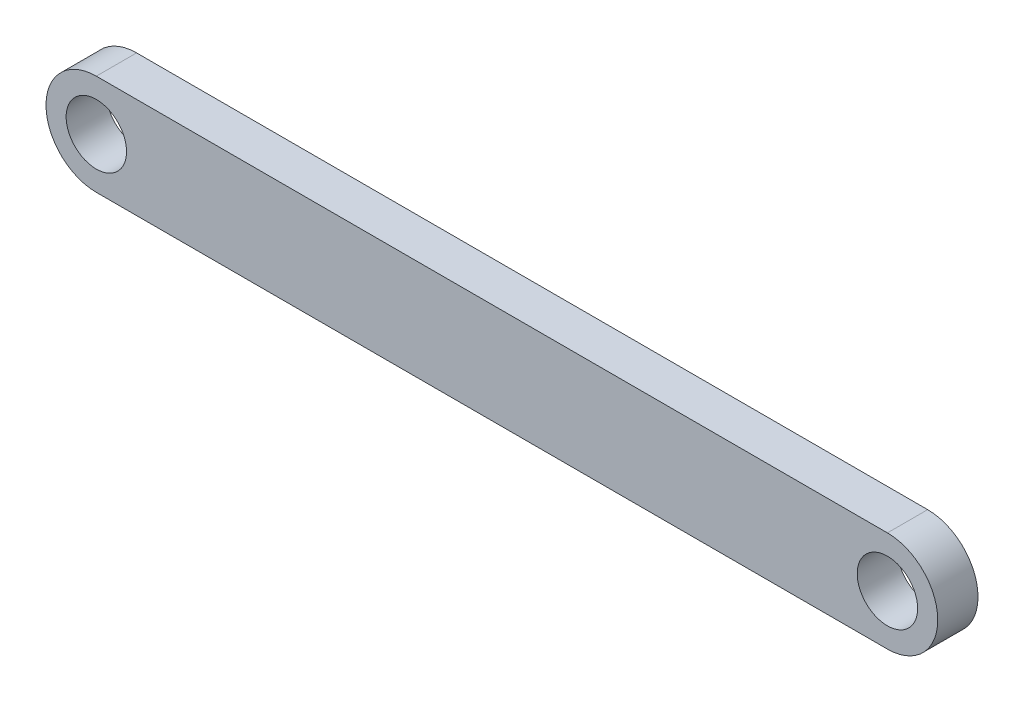
SolidWorks part; units mm, degrees
ref_plane "Front Plane" through (0, 0, 0) normal (0, 0, 1) x (1, 0, 0)
ref_plane "Top Plane" through (0, 0, 0) normal (0, 1, 0) x (1, 0, 0)
ref_plane "Right Plane" through (0, 0, 0) normal (1, 0, 0) x (0, 0, -1)
sketch "Sketch1" plane through (0, 0, 0) normal (0, 0, 1) x (1, 0, 0)
  line L0 (0.0129, 0.0648) -> (39.3129, 0.0648) construction
  line L1 (0.0129, 2.5648) -> (39.3129, 2.5648)
  line L2 (0.0129, -2.4352) -> (39.3129, -2.4352)
  arc A0 (0.0129, 2.5648) -> (0.0129, -2.4352) centre (0.0129, 0.0648) ccw
  arc A1 (39.3129, -2.4352) -> (39.3129, 2.5648) centre (39.3129, 0.0648) ccw
  circle A2 centre (0.0129, 0.0648) radius 1.5
  circle A3 centre (39.3129, 0.0648) radius 1.5
  point P2 (19.6629, 0.0648)
  dimension "D3" = 3
  dimension "D4" = 3
  dimension "D1" = 39.3
  dimension "D2" = 5
extrude "Boss-Extrude1" add sketch "Sketch1" along normal blind 2 contours L2 A1 L1 A0 | A2 | A3
